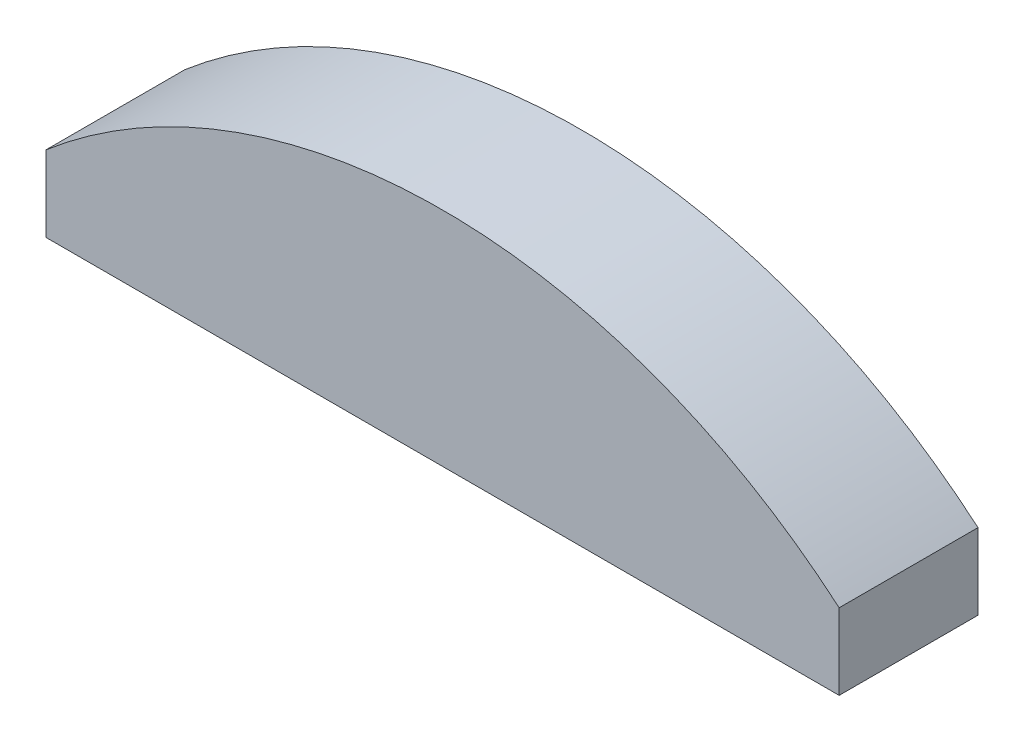
SolidWorks part; units mm, degrees
ref_plane "Alzado" through (0, 0, 0) normal (0, 0, 1) x (1, 0, 0)
ref_plane "Planta" through (0, 0, 0) normal (0, 1, 0) x (1, 0, 0)
ref_plane "Vista lateral" through (0, 0, 0) normal (1, 0, 0) x (0, 0, -1)
sketch "Croquis2" plane through (0, 0, 0) normal (0, 0, 1) x (1, 0, 0)
  line L0 (28.5657, 28) -> (28.5657, 33.4664)
  line L1 (0, 28) -> (0, 40) construction
  line L6 (-28.5657, 28) -> (28.5657, 28)
  line L7 (-28.5657, 28) -> (-28.5657, 33.4664)
  arc A0 (28.5657, 28) -> (-28.5657, 28) centre (0, 0) ccw construction
  arc A1 (28.5657, 33.4664) -> (-28.5657, 33.4664) centre (0, 0) ccw
  point P7 (0, 0)
  point P8 (0, 0)
  point P11 (0, 2.5)
  dimension "D1" = 40
  dimension "D3" = 44
  dimension "D2" = 12
extrude "Saliente-Extruir1" add sketch "Croquis2" along normal mid plane 10
